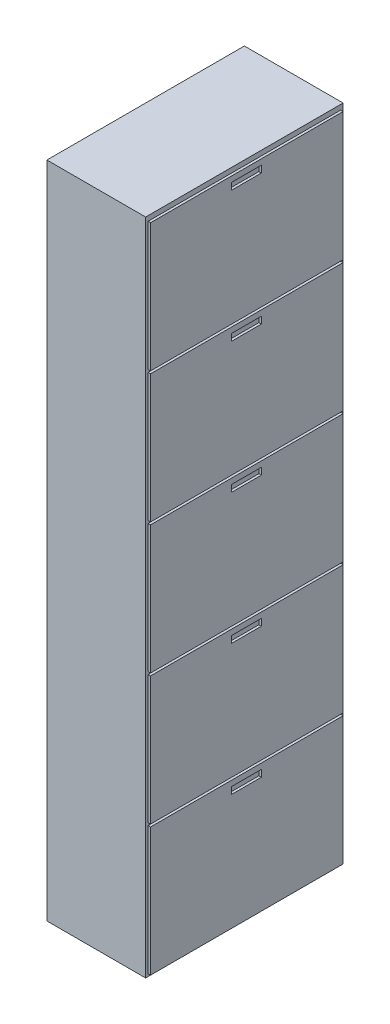
SolidWorks part; units mm, degrees
ref_plane "Front Plane" through (0, 0, 0) normal (0, 0, 1) x (1, 0, 0)
ref_plane "Top Plane" through (0, 0, 0) normal (0, 1, 0) x (1, 0, 0)
ref_plane "Right Plane" through (0, 0, 0) normal (1, 0, 0) x (0, 0, -1)
sketch "Sketch1" plane through (0, 0, 0) normal (0, 0, 1) x (1, 0, 0)
  line L0 (263.062, 4179.9863) -> (-136.938, 4179.9863)
  line L1 (-136.938, 4179.9863) -> (-136.938, 1509.9863)
  line L2 (-136.938, 1509.9863) -> (263.062, 1509.9863)
  line L5 (263.062, 1509.9863) -> (263.062, 4179.9863)
  dimension "D1" = 400
  dimension "D2" = 2670
extrude "Boss-Extrude1" add sketch "Sketch1" along normal blind 800
sketch "Sketch3" plane through (263.062, 0, 0) normal (1, 0, 0) x (0, 0, -1)
  line L0 (-790, 2049.9863) -> (-10, 2049.9863)
  line L1 (-790, 1519.9863) -> (-10, 1519.9863)
  line L2 (-790, 1519.9863) -> (-790, 2039.9863)
  line L3 (-790, 2039.9863) -> (-10, 2039.9863)
  line L4 (-10, 1519.9863) -> (-10, 2039.9863)
  line L5 (-800, 1509.9863) -> (0, 1509.9863) construction
  line L6 (-462.2979, 1989.9863) -> (-341.2251, 1989.9863)
  line L7 (-461.6648, -2274.1108) -> (-340.5919, -2274.1108)
  line L8 (-461.6648, -2274.1108) -> (-461.6648, -2299.9132)
  line L9 (-461.6648, -2299.9132) -> (-340.5919, -2299.9132)
  line L10 (-340.5919, -2274.1108) -> (-340.5919, -2299.9132)
  line L11 (-462.2979, 1989.9863) -> (-462.2979, 2017.4915)
  line L12 (-462.2979, 2017.4915) -> (-341.2251, 2017.4915)
  line L13 (-341.2251, 1989.9863) -> (-341.2251, 2017.4915)
  line L14 (-461.6648, -1727.3383) -> (-340.5919, -1727.3383)
  line L15 (-461.6648, -1753.1407) -> (-340.5919, -1753.1407)
  line L16 (-461.6648, -1727.3383) -> (-461.6648, -1753.1407)
  line L17 (-340.5919, -1727.3383) -> (-340.5919, -1753.1407)
  line L18 (-790, 2049.9863) -> (-790, 2569.9863)
  line L19 (-790, 2569.9863) -> (-10, 2569.9863)
  line L20 (-10, 2049.9863) -> (-10, 2569.9863)
  line L21 (-462.2979, 2519.9863) -> (-341.2251, 2519.9863)
  line L22 (-462.2979, 2519.9863) -> (-462.2979, 2547.4915)
  line L23 (-462.2979, 2547.4915) -> (-341.2251, 2547.4915)
  line L24 (-341.2251, 2519.9863) -> (-341.2251, 2547.4915)
  line L25 (-790, 2579.9863) -> (-10, 2579.9863)
  line L26 (-790, 2579.9863) -> (-790, 3099.9863)
  line L27 (-790, 3099.9863) -> (-10, 3099.9863)
  line L28 (-10, 2579.9863) -> (-10, 3099.9863)
  line L29 (-462.2979, 3049.9863) -> (-341.2251, 3049.9863)
  line L30 (-462.2979, 3049.9863) -> (-462.2979, 3077.4915)
  line L31 (-462.2979, 3077.4915) -> (-341.2251, 3077.4915)
  line L32 (-341.2251, 3049.9863) -> (-341.2251, 3077.4915)
  line L33 (-790, 3109.9863) -> (-10, 3109.9863)
  line L34 (-790, 3109.9863) -> (-790, 3629.9863)
  line L35 (-790, 3629.9863) -> (-10, 3629.9863)
  line L36 (-10, 3109.9863) -> (-10, 3629.9863)
  line L37 (-462.2979, 3579.9863) -> (-341.2251, 3579.9863)
  line L38 (-462.2979, 3579.9863) -> (-462.2979, 3607.4915)
  line L39 (-462.2979, 3607.4915) -> (-341.2251, 3607.4915)
  line L40 (-341.2251, 3579.9863) -> (-341.2251, 3607.4915)
  line L41 (-790, 3639.9863) -> (-10, 3639.9863)
  line L42 (-790, 3639.9863) -> (-790, 4159.9863)
  line L43 (-790, 4159.9863) -> (-10, 4159.9863)
  line L44 (-10, 3639.9863) -> (-10, 4159.9863)
  line L45 (-462.2979, 4109.9863) -> (-341.2251, 4109.9863)
  line L46 (-462.2979, 4109.9863) -> (-462.2979, 4137.4915)
  line L47 (-462.2979, 4137.4915) -> (-341.2251, 4137.4915)
  line L48 (-341.2251, 4109.9863) -> (-341.2251, 4137.4915)
  line L49 (-800, 1509.9863) -> (-800, 4179.9863) construction
  line L50 (0, 1509.9863) -> (0, 4179.9863) construction
  line L116 (-790, 5894.1662) -> (-790, 6414.1662) [skipped]
  line L117 (-790, 6414.1662) -> (-10, 6414.1662) [skipped]
  line L118 (-10, 5894.1662) -> (-10, 6414.1662) [skipped]
  line L119 (-790, 6440.9387) -> (-10, 6440.9387) [skipped]
  line L120 (-790, 6440.9387) -> (-790, 6960.9387) [skipped]
  line L121 (-790, 6960.9387) -> (-10, 6960.9387) [skipped]
  line L122 (-10, 6440.9387) -> (-10, 6960.9387) [skipped]
  line L123 (-790, 6987.7112) -> (-10, 6987.7112) [skipped]
  line L124 (-790, 6987.7112) -> (-790, 7507.7112) [skipped]
  line L125 (-790, 7507.7112) -> (-10, 7507.7112) [skipped]
  line L126 (-10, 6987.7112) -> (-10, 7507.7112) [skipped]
  line L127 (-790, 7534.4837) -> (-10, 7534.4837) [skipped]
  line L128 (-790, 7534.4837) -> (-790, 8054.4837) [skipped]
  line L129 (-790, 8054.4837) -> (-10, 8054.4837) [skipped]
  line L130 (-10, 7534.4837) -> (-10, 8054.4837) [skipped]
  line L131 (-790, 8081.2562) -> (-10, 8081.2562) [skipped]
  line L132 (-790, 8081.2562) -> (-790, 8601.2562) [skipped]
  line L133 (-790, 8601.2562) -> (-10, 8601.2562) [skipped]
  line L134 (-10, 8081.2562) -> (-10, 8601.2562) [skipped]
  line L135 (-790, 8628.0286) -> (-10, 8628.0286) [skipped]
  line L136 (-790, 8628.0286) -> (-790, 9148.0286) [skipped]
  line L137 (-790, 9148.0286) -> (-10, 9148.0286) [skipped]
  line L138 (-10, 8628.0286) -> (-10, 9148.0286) [skipped]
  line L139 (-790, 5347.3937) -> (-790, 5867.3937) [skipped]
  line L140 (-790, 5867.3937) -> (-10, 5867.3937) [skipped]
  line L141 (-10, 5347.3937) -> (-10, 5867.3937) [skipped]
  line L142 (-790, 5894.1662) -> (-10, 5894.1662) [skipped]
  line L143 (-461.6648, 4833.9315) -> (-340.5919, 4833.9315) [skipped]
  line L144 (-461.6648, 4808.1291) -> (-340.5919, 4808.1291) [skipped]
  line L145 (-461.6648, 4833.9315) -> (-461.6648, 4808.1291) [skipped]
  line L146 (-340.5919, 4833.9315) -> (-340.5919, 4808.1291) [skipped]
  line L147 (-790, 5347.3937) -> (-10, 5347.3937) [skipped]
  line L148 (-461.6648, 4287.1591) -> (-340.5919, 4287.1591) [skipped]
  line L149 (-461.6648, 4261.3567) -> (-340.5919, 4261.3567) [skipped]
  line L150 (-461.6648, 4287.1591) -> (-461.6648, 4261.3567) [skipped]
  line L151 (-340.5919, 4287.1591) -> (-340.5919, 4261.3567) [skipped]
  line L152 (-461.6648, -1180.5658) -> (-340.5919, -1180.5658) [skipped]
  line L153 (-461.6648, -1206.3682) -> (-340.5919, -1206.3682) [skipped]
  line L154 (-461.6648, -1180.5658) -> (-461.6648, -1206.3682) [skipped]
  line L155 (-340.5919, -1180.5658) -> (-340.5919, -1206.3682) [skipped]
  line L156 (-461.6648, -633.7933) -> (-340.5919, -633.7933) [skipped]
  line L157 (-461.6648, -659.5957) -> (-340.5919, -659.5957) [skipped]
  line L158 (-461.6648, -633.7933) -> (-461.6648, -659.5957) [skipped]
  line L159 (-340.5919, -633.7933) -> (-340.5919, -659.5957) [skipped]
  line L160 (-461.6648, -87.0208) -> (-340.5919, -87.0208) [skipped]
  line L161 (-461.6648, -112.8232) -> (-340.5919, -112.8232) [skipped]
  line L162 (-461.6648, -87.0208) -> (-461.6648, -112.8232) [skipped]
  line L163 (-340.5919, -87.0208) -> (-340.5919, -112.8232) [skipped]
  line L164 (-790, 2066.7588) -> (-10, 2066.7588) [skipped]
  line L165 (-790, 2066.7588) -> (-790, 2586.7588) [skipped]
  line L166 (-790, 2586.7588) -> (-10, 2586.7588) [skipped]
  line L167 (-10, 2066.7588) -> (-10, 2586.7588) [skipped]
  line L168 (-790, 2613.5313) -> (-10, 2613.5313) [skipped]
  line L169 (-790, 2613.5313) -> (-790, 3133.5313) [skipped]
  line L170 (-790, 3133.5313) -> (-10, 3133.5313) [skipped]
  line L171 (-10, 2613.5313) -> (-10, 3133.5313) [skipped]
  line L172 (-790, 3160.3038) -> (-10, 3160.3038) [skipped]
  line L173 (-790, 3160.3038) -> (-790, 3680.3038) [skipped]
  line L174 (-790, 3680.3038) -> (-10, 3680.3038) [skipped]
  line L175 (-10, 3160.3038) -> (-10, 3680.3038) [skipped]
  line L176 (-790, 3707.0763) -> (-10, 3707.0763) [skipped]
  line L177 (-790, 3707.0763) -> (-790, 4227.0763) [skipped]
  line L178 (-790, 4227.0763) -> (-10, 4227.0763) [skipped]
  line L179 (-10, 3707.0763) -> (-10, 4227.0763) [skipped]
  line L180 (-790, 4253.8488) -> (-10, 4253.8488) [skipped]
  line L181 (-790, 4253.8488) -> (-790, 4773.8488) [skipped]
  line L182 (-790, 4773.8488) -> (-10, 4773.8488) [skipped]
  line L183 (-10, 4253.8488) -> (-10, 4773.8488) [skipped]
  line L184 (-790, 4800.6212) -> (-10, 4800.6212) [skipped]
  line L185 (-790, 4800.6212) -> (-790, 5320.6212) [skipped]
  line L186 (-790, 5320.6212) -> (-10, 5320.6212) [skipped]
  line L187 (-10, 4800.6212) -> (-10, 5320.6212) [skipped]
  line L188 (-461.6648, 2100.0691) -> (-340.5919, 2100.0691) [skipped]
  line L189 (-461.6648, 2100.0691) -> (-461.6648, 2074.2667) [skipped]
  line L190 (-340.5919, 2100.0691) -> (-340.5919, 2074.2667) [skipped]
  line L191 (-461.6648, 2646.8416) -> (-340.5919, 2646.8416) [skipped]
  line L192 (-461.6648, 2621.0392) -> (-340.5919, 2621.0392) [skipped]
  line L193 (-461.6648, 2646.8416) -> (-461.6648, 2621.0392) [skipped]
  line L194 (-340.5919, 2646.8416) -> (-340.5919, 2621.0392) [skipped]
  line L195 (-461.6648, 3193.6141) -> (-340.5919, 3193.6141) [skipped]
  line L196 (-461.6648, 3167.8117) -> (-340.5919, 3167.8117) [skipped]
  line L197 (-461.6648, 3193.6141) -> (-461.6648, 3167.8117) [skipped]
  line L198 (-340.5919, 3193.6141) -> (-340.5919, 3167.8117) [skipped]
  line L199 (-461.6648, 3740.3866) -> (-340.5919, 3740.3866) [skipped]
  line L200 (-461.6648, 3714.5842) -> (-340.5919, 3714.5842) [skipped]
  line L201 (-461.6648, 3740.3866) -> (-461.6648, 3714.5842) [skipped]
  line L202 (-340.5919, 3740.3866) -> (-340.5919, 3714.5842) [skipped]
  line L203 (-461.6648, 2074.2667) -> (-340.5919, 2074.2667) [skipped]
  line L204 (-461.6648, 459.7517) -> (-340.5919, 459.7517) [skipped]
  line L205 (-461.6648, 433.9492) -> (-340.5919, 433.9492) [skipped]
  line L206 (-461.6648, 459.7517) -> (-461.6648, 433.9492) [skipped]
  line L207 (-340.5919, 459.7517) -> (-340.5919, 433.9492) [skipped]
  line L208 (-461.6648, 1006.5241) -> (-340.5919, 1006.5241) [skipped]
  line L209 (-461.6648, 980.7217) -> (-340.5919, 980.7217) [skipped]
  line L210 (-461.6648, 1006.5241) -> (-461.6648, 980.7217) [skipped]
  line L211 (-340.5919, 1006.5241) -> (-340.5919, 980.7217) [skipped]
  line L212 (-461.6648, 1553.2966) -> (-340.5919, 1553.2966) [skipped]
  line L213 (-461.6648, 1527.4942) -> (-340.5919, 1527.4942) [skipped]
  line L214 (-461.6648, 1553.2966) -> (-461.6648, 1527.4942) [skipped]
  line L215 (-340.5919, 1553.2966) -> (-340.5919, 1527.4942) [skipped]
  dimension "D1" = 520
  dimension "D2" = 5
  dimension "D3" = 10
  dimension "D4" = 14
  dimension "D6" = 50
  dimension "D7" = 10
  dimension "D5" = 10
  dimension "D8" = 10
extrude "Boss-Extrude3" add sketch "Sketch3" along normal blind 10
equation "\"Ab\"=10"
equation "\"D3@Sketch3\"=\"Ab\""
equation "\"D5@Sketch3\"=\"Ab\""
equation "\"D7@Sketch3\"=\"Ab\""
equation "\"D8@Sketch3\"=\"Ab\""
